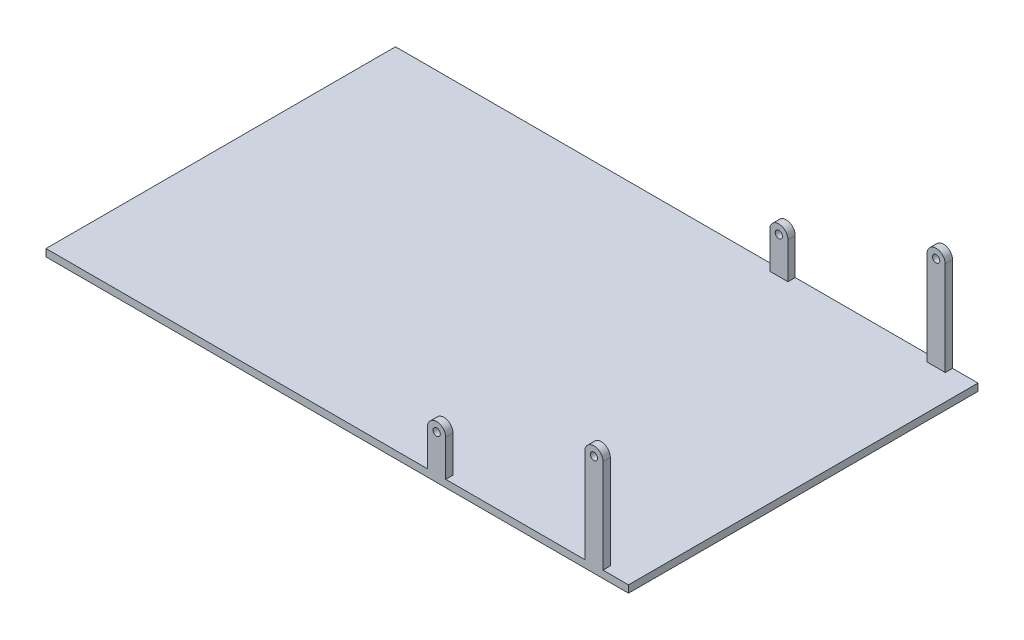
SolidWorks part; units mm, degrees
material "Alloy Steel"
ref_plane "Front Plane" through (0, 0, 0) normal (0, 0, 1) x (1, 0, 0)
ref_plane "Top Plane" through (0, 0, 0) normal (0, 1, 0) x (1, 0, 0)
ref_plane "Right Plane" through (0, 0, 0) normal (1, 0, 0) x (0, 0, -1)
sketch "Sketch1" plane through (0, 0, 0) normal (0, 1, 0) x (1, 0, 0)
  line L1 (-800, 480) -> (800, 480)
  line L2 (-800, 480) -> (-800, -480)
  line L3 (-800, -480) -> (800, -480)
  line L4 (800, 480) -> (800, -480)
  line L5 (-800, 480) -> (800, -480) construction
  line L6 (-800, -480) -> (800, 480) construction
  point P0 (0, 0)
  dimension "D1" = 960
  dimension "D2" = 1600
extrude "Boss-Extrude1" add sketch "Sketch1" against normal blind 20
sketch "Sketch2" plane through (0, 0, 480) normal (0, 0, 1) x (1, 0, 0)
  line L0 (298, 0) -> (298, 100)
  line L1 (-800, 0) -> (800, 0) construction
  line L2 (248, 0) -> (248, 100)
  line L3 (730, 0) -> (730, 258.2)
  line L4 (680, 0) -> (680, 258.2)
  line L5 (800, -20) -> (800, 0) construction
  arc A0 (248, 100) -> (298, 100) centre (273, 100) cw
  arc A1 (680, 258.2) -> (730, 258.2) centre (705, 258.2) cw
  circle A2 centre (273, 100) radius 10
  circle A3 centre (705, 258.2) radius 10
  line M3 (800, 0) -> (-800, 0)
  dimension "D1" = 25
  dimension "D2" = 25
  dimension "D6" = 20
  dimension "D7" = 20
  dimension "D3" = 70
  dimension "D4" = 432
  dimension "D5" = 158.2
  dimension "D8" = 100
extrude "Boss-Extrude2" add sketch "Sketch2" against normal blind 20 contours A0 L2 L0 A2 M3 | A1 L4 L3 A3 M3
mirror "Mirror1" about plane through (0, 0, 0) normal (0, 0, 1) of bodies 102
